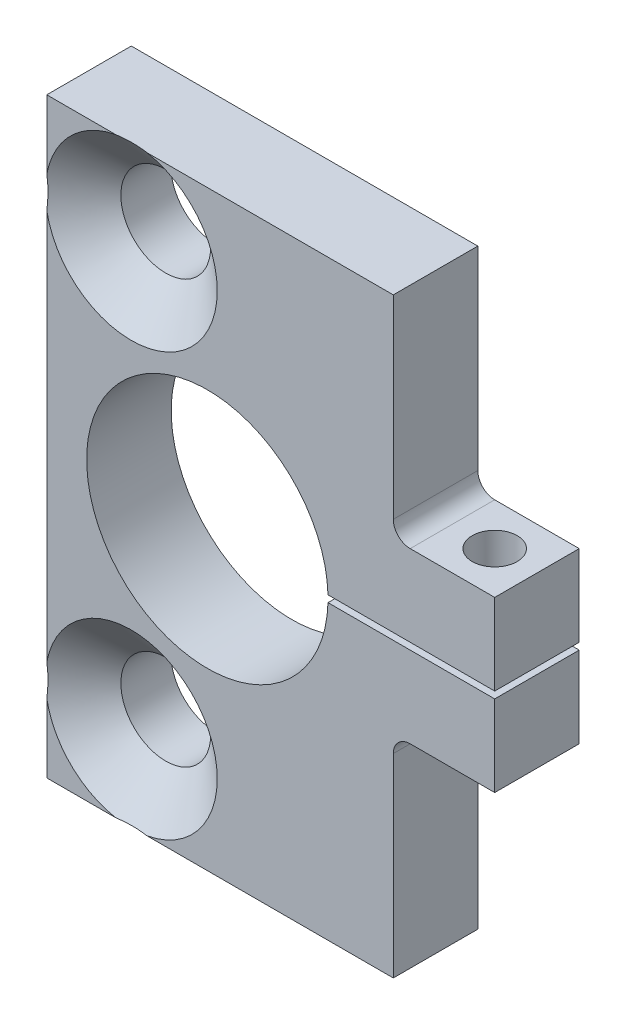
SolidWorks part; units mm, degrees
material "6061-T6 (SS)"
ref_plane "Front Plane" through (0, 0, 0) normal (0, 0, 1) x (1, 0, 0)
ref_plane "Top Plane" through (0, 0, 0) normal (0, 1, 0) x (1, 0, 0)
ref_plane "Right Plane" through (0, 0, 0) normal (1, 0, 0) x (0, 0, -1)
sketch "Sketch1" plane through (0, 0, 0) normal (0, 0, 1) x (1, 0, 0)
  line L1 (-33.655, -44.45) -> (33.655, -44.45)
  line L2 (-33.655, -44.45) -> (-33.655, 44.45)
  line L3 (-33.655, 44.45) -> (33.655, 44.45)
  line L4 (33.655, -44.45) -> (33.655, 44.45)
  line L5 (-33.655, -44.45) -> (33.655, 44.45) construction
  line L6 (-33.655, 44.45) -> (33.655, -44.45) construction
  point P0 (0, 0)
  dimension "D1" = 67.31
  dimension "D2" = 88.9
extrude "Extrude1" add sketch "Sketch1" along normal blind 12.7
sketch "Sketch2" plane through (0, 0, 12.7) normal (0, 0, 1) x (1, 0, 0)
  line L0 (-9.525, 0) -> (-33.655, 0) construction
  line L5 (-33.655, 44.45) -> (-33.655, -44.45) construction
  circle A0 centre (-9.525, 0) radius 18.1356
  dimension "D1" = 36.2712
  dimension "D2" = 24.13
extrude "Extrude2" cut sketch "Sketch2" against normal through all
sketch "Sketch3" plane through (0, 0, 12.7) normal (0, 0, 1) x (1, 0, 0)
  line L0 (8.6106, 0) -> (33.655, 0) construction
  line L1 (33.655, -44.45) -> (33.655, 44.45) construction
  line L3 (6.8985, -0.508) -> (35.3671, -0.508)
  line L4 (6.8985, -0.508) -> (6.8985, 0.508)
  line L5 (6.8985, 0.508) -> (35.3671, 0.508)
  line L6 (35.3671, -0.508) -> (35.3671, 0.508)
  line L7 (6.8985, -0.508) -> (35.3671, 0.508) construction
  line L8 (6.8985, 0.508) -> (35.3671, -0.508) construction
  circle A0 centre (-9.525, 0) radius 18.1356 construction
  point P6 (21.1328, 0)
  dimension "D1" = 1.016
extrude "Extrude3" cut sketch "Sketch3" against normal through all
sketch "Sketch4" plane through (0, 44.45, 0) normal (0, 1, 0) x (1, 0, 0)
  line L0 (33.655, -6.35) -> (27.305, -6.35) construction
  line L1 (33.655, -12.7) -> (33.655, 0) construction
  dimension "D1" = 6.35
hole_wizard "1/4 Clearance Hole1" positions "3DSketch1" profile "Sketch5" hole size "1/4" standard "Ansi Inch" end condition through all
sketch3d "3DSketch1"
  point P0 (27.305, 44.45, 6.35)
sketch "Sketch5" plane through (27.305, 44.45, 6.35) normal (1, 0, 0) x (0, 0, 1)
  line L0 (0, 0) -> (0, 88.9)
  line L1 (0, 88.9) -> (3.3782, 88.9)
  line L2 (3.3782, 88.9) -> (3.3782, 0)
  line L5 (3.3782, 0) -> (0, 0)
  line L11 (0, -6.35) -> (0, 107.95) construction
  dimension "Thru Hole Dia." = 6.7564
  dimension "Thru Hole Depth" = 88.9
sketch "Sketch6" plane through (0, -44.45, 0) normal (0, -1, 0) x (1, 0, 0)
  line L0 (-33.655, 6.35) -> (-27.305, 6.35) construction
  line L1 (-33.655, 12.7) -> (-33.655, 0) construction
  dimension "D1" = 6.35
hole_wizard "Tap Drill for 1/4-20 Tap1" positions "3DSketch2" profile "Sketch7" hole size "1/4-20" standard "Ansi Inch"
sketch3d "3DSketch2"
  point P0 (-31.75, -38.1, 4.7625)
sketch "Sketch7" plane through (-31.75, -38.1, 4.7625) normal (1, 0, 0) x (0, 0, -1)
  line L0 (0, 0) -> (0, 19.3138)
  line L1 (0, 19.3138) -> (2.5527, 17.78)
  line L2 (2.5527, 17.78) -> (2.5527, 0)
  line L5 (2.5527, 0) -> (0, 0)
  line L10 (0, 19.3138) -> (-2.5527, 17.78) construction
  line L11 (0, -6.35) -> (0, 107.95) construction
  dimension "Hole Dia." = 5.1054
  dimension "Hole Depth" = 17.78
  dimension "Drill Angle" = 118
sketch "Sketch8" plane through (0, 0, 12.7) normal (0, 0, 1) x (1, 0, 0)
  line L0 (-33.655, 31.75) -> (-20.955, 31.75) construction
  line L1 (-33.655, 44.45) -> (-33.655, -44.45) construction
  line L2 (33.655, 44.45) -> (-33.655, 44.45) construction
  dimension "D1" = 12.7
  dimension "D2" = 12.7
hole_wizard "CSK for 1/2 Flat Head Machine Screw (100)1" positions "3DSketch3" profile "Sketch9" countersink size "1/2" standard "Ansi Inch" end condition through all
sketch3d "3DSketch3"
  point P0 (-20.955, 31.75, 12.7)
sketch "Sketch9" plane through (-20.955, 31.75, 12.7) normal (1, 0, 0) x (0, -1, 0)
  line L0 (0, 0) -> (0, 12.7)
  line L1 (0, 12.7) -> (6.7462, 12.7)
  line L2 (6.7462, 12.7) -> (6.7462, 5.177)
  line L3 (6.7462, 5.177) -> (12.9159, 0)
  line L5 (12.9159, 0) -> (0, 0)
  line L6 (-6.7462, 5.177) -> (-12.9159, 0) construction
  line L11 (0, -6.35) -> (0, 107.95) construction
  dimension "Thru Hole Dia." = 13.4925
  dimension "Thru Hole Depth" = 12.7
  dimension "Near C'Sink Dia." = 25.8318
  dimension "Near C'Sink Angle" = 100
mirror "Mirror1" about plane through (0, 0, 0) normal (0, 1, 0) of "CSK for 1/2 Flat Head Machine Screw (100)1"
sketch "Sketch10" plane through (0, 0, 12.7) normal (0, 0, 1) x (1, 0, 0)
  line L1 (33.655, 44.45) -> (18.415, 44.45)
  line L2 (33.655, 44.45) -> (33.655, 12.7)
  line L3 (33.655, 12.7) -> (18.415, 12.7)
  line L4 (18.415, 44.45) -> (18.415, 12.7)
  dimension "D1" = 15.24
  dimension "D2" = 31.75
extrude "Extrude4" cut sketch "Sketch10" against normal through all
fillet "Fillet1" radius 2.54 1 edges at (18.415, 12.7, 6.35)
mirror "Mirror2" about plane through (0, 0, 0) normal (0, 1, 0) of "Fillet1", "Extrude4"
ref_plane "Plane1" through (0, 0, 19.05) normal (0, 0, 1) x (1, 0, 0)
sketch "Sketch11" plane through (0, 0, 19.05) normal (0, 0, 1) x (1, 0, 0)
  point P0 (-33.655, -44.45)
